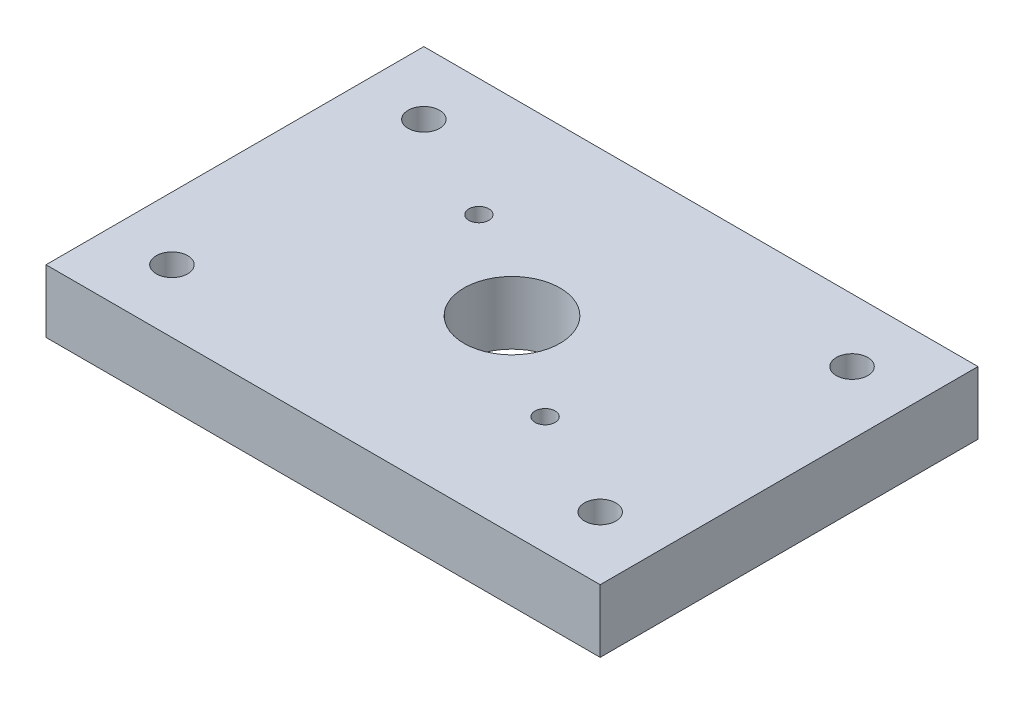
SolidWorks part; units mm, degrees
ref_plane "Front Plane" through (0, 0, 0) normal (0, 0, 1) x (1, 0, 0)
ref_plane "Top Plane" through (0, 0, 0) normal (0, 1, 0) x (1, 0, 0)
ref_plane "Right Plane" through (0, 0, 0) normal (1, 0, 0) x (0, 0, -1)
sketch "Sketch1" plane through (0, 0, 0) normal (0, 1, 0) x (1, 0, 0)
  line L1 (55.88, -38.1) -> (-55.88, -38.1)
  line L2 (55.88, -38.1) -> (55.88, 38.1)
  line L3 (55.88, 38.1) -> (-55.88, 38.1)
  line L4 (-55.88, -38.1) -> (-55.88, 38.1)
  line L5 (55.88, -38.1) -> (-55.88, 38.1) construction
  line L6 (55.88, 38.1) -> (-55.88, -38.1) construction
  circle A0 centre (0, 0) radius 9.6837
  circle A1 centre (-20.9862, 14.3088) radius 2.0193
  circle A2 centre (20.9862, -14.3088) radius 2.0193
  circle A3 centre (0, 0) radius 25.4 construction
  circle A4 centre (-43.18, 25.4) radius 3.175
  circle A5 centre (-43.18, -25.4) radius 3.175
  circle A6 centre (43.18, -25.4) radius 3.175
  circle A7 centre (43.18, 25.4) radius 3.175
  point P0 (0, 0)
  dimension "D3" = 50.8
  dimension "D4" = 4.0386
  dimension "D5" = 19.3675
  dimension "D6" = 6.35
  dimension "D2" = 86.36
  dimension "D7" = 12.7
  dimension "D8" = 12.7
  dimension "D9" = 12.7
  dimension "D10" = 12.7
  dimension "D11" = 50.8
extrude "Boss-Extrude1" add sketch "Sketch1" along normal blind 12.7
